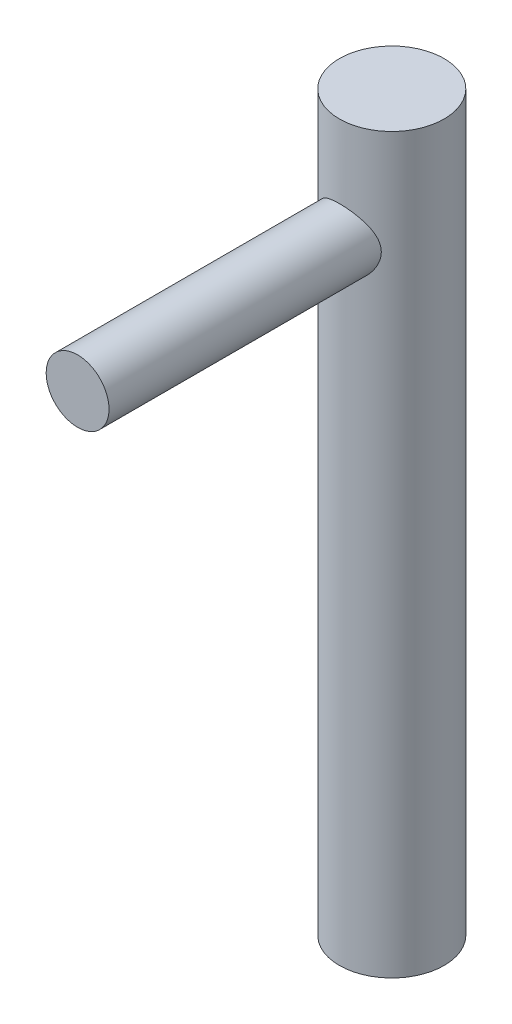
SolidWorks part; units mm, degrees
ref_plane "Front Plane" through (0, 0, 0) normal (0, 0, 1) x (1, 0, 0)
ref_plane "Top Plane" through (0, 0, 0) normal (0, 1, 0) x (1, 0, 0)
ref_plane "Right Plane" through (0, 0, 0) normal (1, 0, 0) x (0, 0, -1)
sketch "Sketch1" plane through (0, 0, 0) normal (0, 1, 0) x (1, 0, 0)
  circle A0 centre (0, 0) radius 2.5
  dimension "D1" = 5
extrude "Boss-Extrude1" add sketch "Sketch1" along normal blind 35
sketch "Sketch4" plane through (0, 0, 0) normal (0, 0, 1) x (1, 0, 0)
  line L0 (2.5, 35) -> (-2.5, 35) construction
  line L1 (0, 30) -> (0, 35) construction
  circle A0 centre (0, 30) radius 1.5
  dimension "D1" = 3
  dimension "D2" = 5
extrude "Boss-Extrude3" add sketch "Sketch4" along normal blind 15
sketch "Sketch5" plane through (0, 0, 0) normal (0, -1, 0) x (1, 0, 0)
  line L0 (-1, 2.2913) -> (-1, -2.2913)
  arc A0 (1.5, 2) -> (-1.5, 2) centre (0, 0) ccw construction
  circle A1 centre (0, 0) radius 2.5 construction
  dimension "D1" = 1
